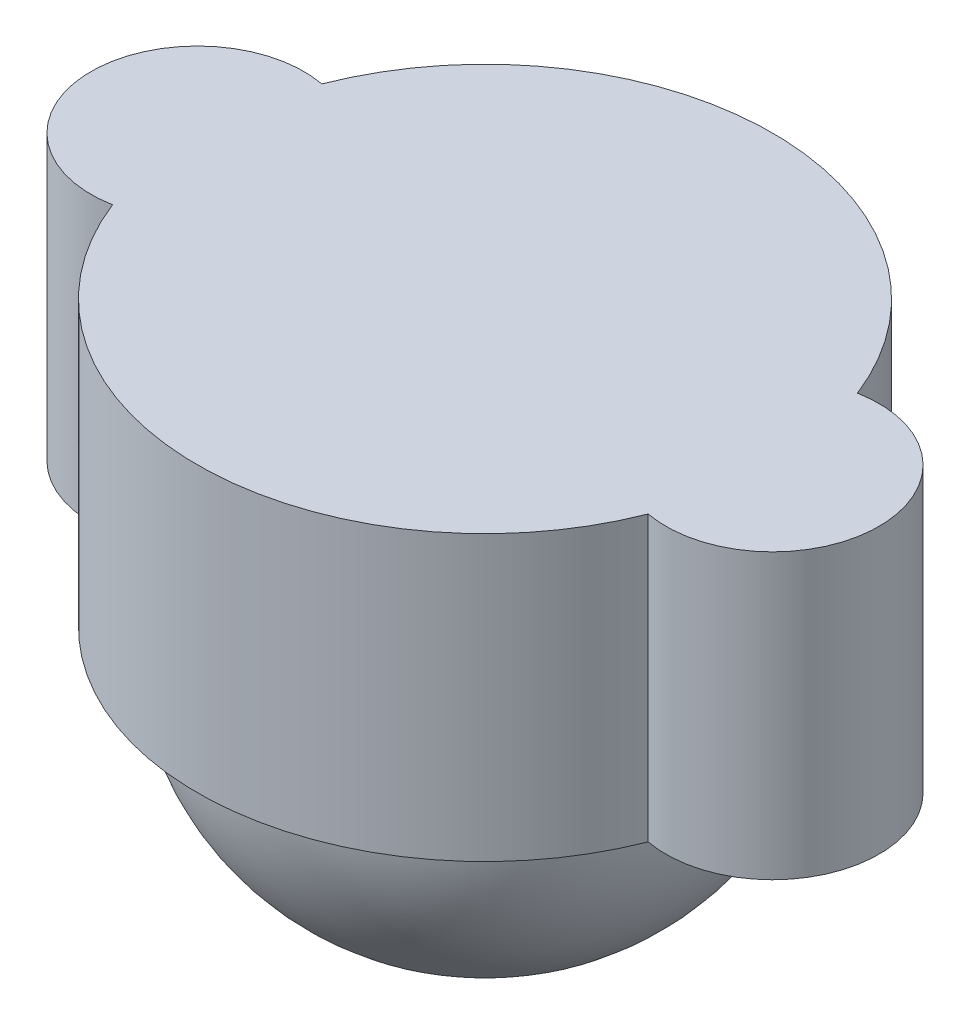
SolidWorks part; units mm, degrees
ref_plane "Front Plane" through (0, 0, 0) normal (0, 0, 1) x (1, 0, 0)
ref_plane "Top Plane" through (0, 0, 0) normal (0, 1, 0) x (1, 0, 0)
ref_plane "Right Plane" through (0, 0, 0) normal (1, 0, 0) x (0, 0, -1)
sketch "Sketch2" plane through (0, 0, 0) normal (0, 1, 0) x (1, 0, 0)
  arc A0 (-7.5444, -2.9481) -> (7.5444, -2.9481) centre (0, 0) ccw
  arc A1 (7.5444, -2.9481) -> (7.5444, 2.9481) centre (8.1, 0) ccw
  arc A2 (-7.5444, 2.9481) -> (-7.5444, -2.9481) centre (-8.1, 0) ccw
  arc A3 (7.5444, 2.9481) -> (-7.5444, 2.9481) centre (0, 0) ccw
  dimension "D1" = 3
  dimension "D2" = 16.2
extrude "Boss-Extrude1" add sketch "Sketch2" against normal blind 8
sketch "Sketch3" plane through (0, -8, 0) normal (0, -1, 0) x (1, 0, 0)
  line L0 (0, 7) -> (0, -7)
  arc A0 (0, 7) -> (0, -7) centre (0, 0) ccw
  dimension "D1" = 14
revolve "Revolve1" add sketch "Sketch3" angle 360 about L0
